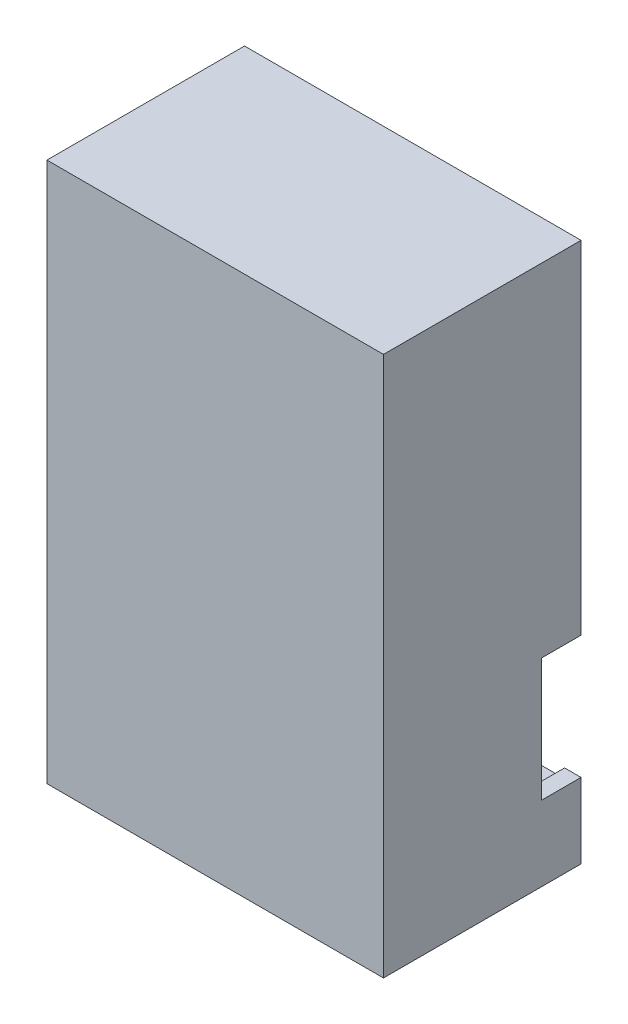
SolidWorks part; units mm, degrees
ref_plane "Front Plane" through (0, 0, 0) normal (0, 0, 1) x (1, 0, 0)
ref_plane "Top Plane" through (0, 0, 0) normal (0, 1, 0) x (1, 0, 0)
ref_plane "Right Plane" through (0, 0, 0) normal (1, 0, 0) x (0, 0, -1)
sketch "Sketch1" plane through (0, 0, 0) normal (0, 0, 1) x (1, 0, 0)
  line L0 (0, 41) -> (51.1, 41) construction
  line L1 (0, 0) -> (51.1, 0)
  line L2 (0, 0) -> (0, 82)
  line L3 (0, 82) -> (51.1, 82)
  line L4 (51.1, 0) -> (51.1, 82)
  line L5 (25.55, 82) -> (25.55, 41) construction
  line L6 (6, 72.05) -> (2.5, 72.05)
  line L7 (2.5, 72.05) -> (2.5, 9.95)
  line L8 (9.95, 76) -> (9.95, 79.5)
  line L9 (9.95, 79.5) -> (41.15, 79.5)
  line L10 (48.6, 72.05) -> (48.6, 9.95)
  line L11 (45.1, 72.05) -> (48.6, 72.05)
  line L12 (41.15, 76) -> (41.15, 79.5)
  line L13 (6, 9.95) -> (2.5, 9.95)
  line L14 (9.95, 6) -> (9.95, 2.5)
  line L15 (9.95, 2.5) -> (41.15, 2.5)
  line L16 (41.15, 6) -> (41.15, 2.5)
  line L17 (45.1, 9.95) -> (48.6, 9.95)
  circle A0 centre (6, 76) radius 1.45
  circle A1 centre (45.1, 76) radius 1.45
  circle A2 centre (45.1, 6) radius 1.45
  circle A3 centre (6, 6) radius 1.45
  arc A4 (6, 72.05) -> (9.95, 76) centre (6, 76) ccw
  arc A5 (45.1, 72.05) -> (41.15, 76) centre (45.1, 76) cw
  arc A6 (6, 9.95) -> (9.95, 6) centre (6, 6) cw
  arc A7 (45.1, 9.95) -> (41.15, 6) centre (45.1, 6) ccw
  point P26 (2.5, 41)
  point P28 (25.55, 79.5)
  point P36 (48.6, 41)
  dimension "D3" = 2.9
  dimension "D6" = 2.5
  dimension "D1" = 51.1
  dimension "D2" = 82
  dimension "D4" = 6
  dimension "D5" = 6
  dimension "D7" = 2.5
  dimension "D8" = 2.5
extrude "Boss-Extrude1" add sketch "Sketch1" along normal blind 5
sketch "Sketch2" plane through (0, 0, 0) normal (0, 0, 1) x (1, 0, 0)
  line L0 (0, 0) -> (51.1, 0) construction
  line L1 (0, 82) -> (51.1, 82)
  line L2 (0, 82) -> (0, 0)
  line L3 (0, 0) -> (51.1, 0)
  line L4 (51.1, 82) -> (51.1, 0)
  line L5 (51.1, 0) -> (51.1, 82) construction
  line L6 (41.15, 2.5) -> (49.111, 2.5) construction
  line L7 (2.5, 72.05) -> (2.5, 80.3457) construction
  line L8 (48.6, 9.95) -> (48.6, 2.5) construction
  line L9 (2.5, 80.3457) -> (9.95, 79.5) construction
  line L10 (9.95, 79.5) -> (2.5, 79.5) construction
  line L12 (2.5, 79.5) -> (48.6, 79.5)
  line L13 (2.5, 79.5) -> (2.5, 2.5)
  line L14 (2.5, 2.5) -> (48.6, 2.5)
  line L15 (48.6, 79.5) -> (48.6, 2.5)
extrude "Boss-Extrude2" add sketch "Sketch2" along normal blind 23 from surface at 5 starting at face at (4.55, 6, 5)
sketch "Sketch4" plane through (0, 0, 0) normal (1, 0, 0) x (0, 0, -1)
  line L1 (-28, 82) -> (-30, 82)
  line L2 (-28, 82) -> (-28, 0)
  line L3 (-28, 0) -> (-30, 0)
  line L4 (-30, 82) -> (-30, 0)
  dimension "D1" = 2
extrude "Boss-Extrude3" add sketch "Sketch4" along normal up to surface (51.1 mm away) from surface at 0 up to face at (51.1, 41, 14) starting at face at (0, 41, 14)
sketch "Sketch5" plane through (0, 0, 0) normal (0, 0, 1) x (1, 0, 0)
  line L0 (51.1, 0) -> (51.1, 82) construction
  line L1 (51.1, 11.376) -> (48.6, 11.376)
  line L2 (51.1, 11.376) -> (51.1, 30.076)
  line L3 (51.1, 30.076) -> (48.6, 30.076)
  line L4 (48.6, 11.376) -> (48.6, 30.076)
  line L5 (48.6, 2.5) -> (48.6, 79.5) construction
  dimension "D1" = 18.7
extrude "Cut-Extrude1" cut sketch "Sketch5" along normal blind 6
sketch "Sketch6" plane through (0, 0, 0) normal (0, 0, 1) x (1, 0, 0)
  line L0 (48.6, 30.076) -> (2.5, 30.076) construction
  line L1 (2.5, 79.5) -> (2.5, 2.5) construction
  line L2 (48.6, 30.076) -> (48.6, 11.376) construction
  line L3 (48.6, 11.376) -> (2.5, 11.376) construction
  line L4 (2.5, 72.05) -> (2.5, 9.95) construction
  line L5 (2.5, 30.076) -> (10.6, 30.076)
  line L6 (2.5, 30.076) -> (2.5, 11.376)
  line L7 (2.5, 11.376) -> (10.6, 11.376)
  line L8 (10.6, 30.076) -> (10.6, 11.376)
  dimension "D1" = 38
extrude "Boss-Extrude4" add sketch "Sketch6" along normal blind 2 from offset 5
sketch "Sketch7" plane through (0, 0, 0) normal (0, 0, 1) x (1, 0, 0)
  line L0 (2.5, 72.05) -> (2.5, 9.95) construction
  line L1 (10.6, 30.076) -> (2.5, 30.076)
  line L2 (10.6, 30.076) -> (10.6, 32.076)
  line L3 (10.6, 32.076) -> (2.5, 32.076)
  line L4 (2.5, 30.076) -> (2.5, 32.076)
  line L5 (2.5, 79.5) -> (2.5, 2.5) construction
  line L6 (10.6, 11.376) -> (2.5, 11.376)
  line L7 (10.6, 11.376) -> (10.6, 9.376)
  line L8 (10.6, 9.376) -> (2.5, 9.376)
  line L9 (2.5, 11.376) -> (2.5, 9.376)
  dimension "D1" = 2
  dimension "D2" = 2
extrude "Boss-Extrude5" add sketch "Sketch7" along normal blind 7
